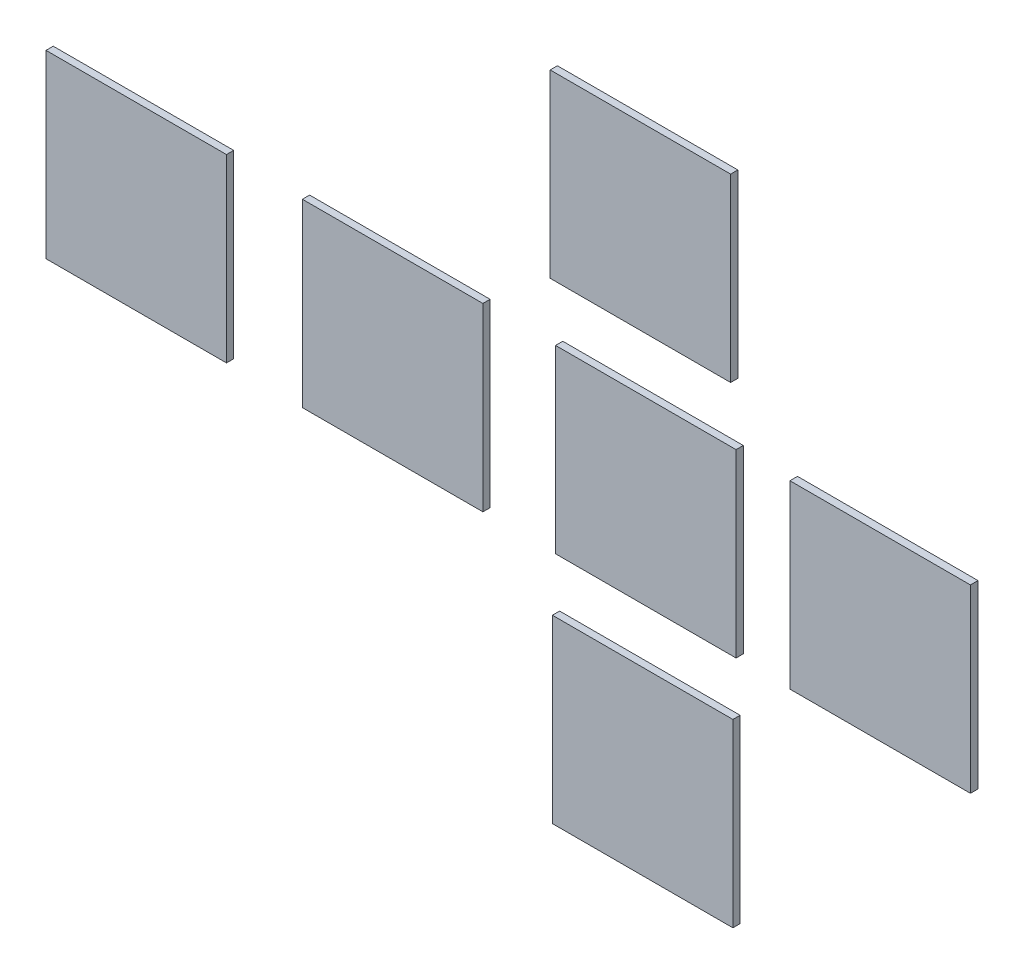
SolidWorks part; units mm, degrees
ref_plane "Alzado" through (0, 0, 0) normal (0, 0, 1) x (1, 0, 0)
ref_plane "Planta" through (0, 0, 0) normal (0, 1, 0) x (1, 0, 0)
ref_plane "Vista lateral" through (0, 0, 0) normal (1, 0, 0) x (0, 0, -1)
sketch "Croquis2" plane through (0, 0, 0) normal (0, 0, 1) x (1, 0, 0)
  line L1 (250, -250) -> (-250, -250)
  line L2 (250, -250) -> (250, 250)
  line L3 (250, 250) -> (-250, 250)
  line L4 (-250, -250) -> (-250, 250)
  line L5 (250, -250) -> (-250, 250) construction
  line L6 (250, 250) -> (-250, -250) construction
  point P0 (0, 0)
extrude "Saliente-Extruir1" add sketch "Croquis2" along normal blind 20 and the other way blind 1 contours L2 L1 L4 L3
sketch "Croquis3" plane through (0, 0, 0) normal (0, 0, 1) x (1, 0, 0)
  line L0 (98.4938, 22.5214) -> (336.9429, 22.5214) construction
  line L1 (-98.9313, 72.6987) -> (-49.598, 72.6987) construction
  line L3 (-899.26, -250) -> (-399.26, -250)
  line L4 (-899.26, -250) -> (-899.26, 250)
  line L5 (-899.26, 250) -> (-399.26, 250)
  line L6 (-399.26, -250) -> (-399.26, 250)
  line L7 (-899.26, -250) -> (-399.26, 250) construction
  line L8 (-899.26, 250) -> (-399.26, -250) construction
  point P4 (-649.26, 0)
  dimension "D1" = 500
  dimension "D2" = 500
extrude "Saliente-Extruir4" add sketch "Croquis3" along normal blind 20 separate body contours L4 L3 L6 L5
sketch "Croquis6" plane through (0, 0, 0) normal (0, 0, 1) x (1, 0, 0)
  line L0 (-2310.9986, -247.9026) -> (-1810.9986, -247.9026)
  line L1 (-2310.9986, -247.9026) -> (-2310.9986, 252.0974)
  line L2 (-1600.6472, -249.9798) -> (-1100.6472, -249.9798)
  line L3 (-1600.6472, -249.9798) -> (-1600.6472, 250.0202)
  line L4 (-1600.6472, 250.0202) -> (-1100.6472, 250.0202)
  line L5 (-1100.6472, -249.9798) -> (-1100.6472, 250.0202)
  line L6 (-1600.6472, -249.9798) -> (-1100.6472, 250.0202) construction
  line L7 (-1600.6472, 250.0202) -> (-1100.6472, -249.9798) construction
  line L8 (-2310.9986, 252.0974) -> (-1810.9986, 252.0974)
  line L9 (-1810.9986, -247.9026) -> (-1810.9986, 252.0974)
  line L10 (-914.252, 403.5106) -> (-414.252, 403.5106)
  line L11 (-914.252, 403.5106) -> (-914.252, 903.5106)
  line L12 (-914.252, 903.5106) -> (-414.252, 903.5106)
  line L13 (-414.252, 403.5106) -> (-414.252, 903.5106)
  line L14 (-908.0367, -901.7041) -> (-408.0367, -901.7041)
  line L15 (-908.0367, -901.7041) -> (-908.0367, -401.7041)
  line L16 (-908.0367, -401.7041) -> (-408.0367, -401.7041)
  line L17 (-408.0367, -901.7041) -> (-408.0367, -401.7041)
  point P1 (-1350.6472, 0.0202)
  dimension "D1" = 500
  dimension "D2" = 500
  dimension "D3" = 500
  dimension "D4" = 500
  dimension "D5" = 500
  dimension "D6" = 500
  dimension "D7" = 500
  dimension "D8" = 500
extrude "Saliente-Extruir8" add sketch "Croquis6" along normal blind 20 separate body contours L10 L13 L12 L11 | L0 L9 L8 L1 | L3 L2 L5 L4 | L14 L17 L16 L15
sketch "Croquis8"
other "Croquis con pluma1" parameters "D1"=630.4559
